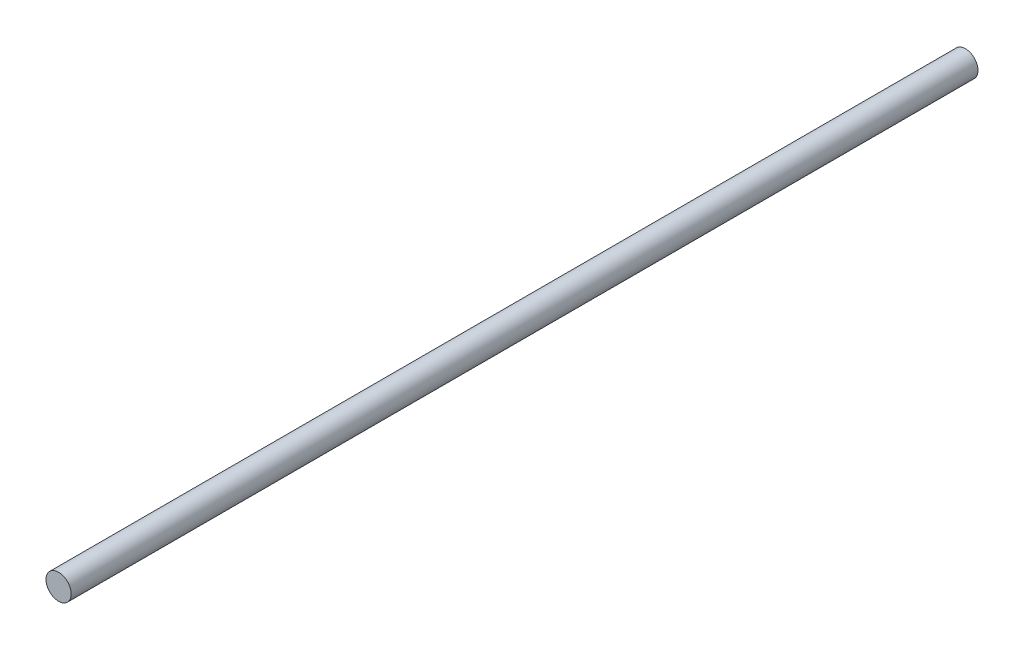
SolidWorks part; units mm, degrees
material "Pine"
ref_plane "Front Plane" through (0, 0, 0) normal (0, 0, 1) x (1, 0, 0)
ref_plane "Top Plane" through (0, 0, 0) normal (0, 1, 0) x (1, 0, 0)
ref_plane "Right Plane" through (0, 0, 0) normal (1, 0, 0) x (0, 0, -1)
sketch "Sketch1" plane through (0, 0, 0) normal (0, 0, 1) x (1, 0, 0)
  circle A0 centre (0, 0) radius 3.175
  dimension "D1" = 6.35
extrude "Boss-Extrude1" add sketch "Sketch1" along normal mid plane 228.6
